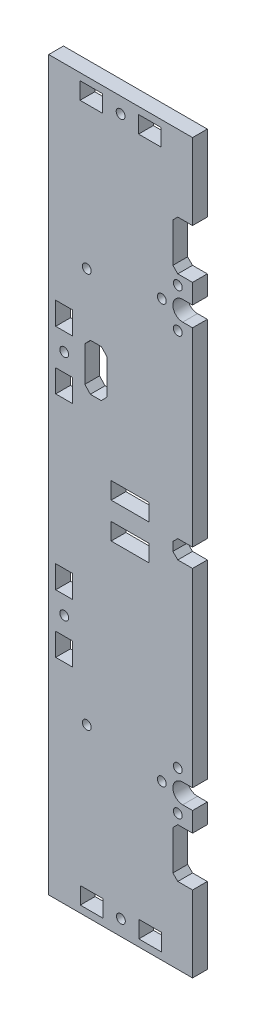
SolidWorks part; units mm, degrees
ref_plane "Plano frontal" through (0, 0, 0) normal (0, 0, 1) x (1, 0, 0)
ref_plane "Plano superior" through (0, 0, 0) normal (0, 1, 0) x (1, 0, 0)
ref_plane "Plano direito" through (0, 0, 0) normal (1, 0, 0) x (0, 0, -1)
sketch "Model" plane through (0, 0, 0) normal (0, 0, 1) x (1, 0, 0)
  line L0 (89.7713, 6.2321) -> (31.2713, 6.2321)
  line L1 (89.7713, 302.232) -> (89.7713, 271.232)
  line L2 (81.7713, 39.2321) -> (81.7713, 55.2321)
  line L3 (89.7713, 57.2321) -> (83.7713, 57.2321)
  line L4 (83.7713, 271.232) -> (89.7713, 271.232)
  line L5 (89.7713, 251.232) -> (89.7713, 243.232)
  line L6 (83.7713, 271.232) -> (81.7713, 269.232)
  line L7 (83.7713, 251.232) -> (89.7713, 251.232)
  line L8 (89.7713, 37.2321) -> (83.7713, 37.2321)
  line L9 (89.7713, 235.232) -> (89.7713, 157.982)
  line L10 (85.7713, 65.2321) -> (89.7713, 65.2321)
  line L11 (81.7713, 253.232) -> (81.7713, 269.232)
  line L12 (83.7713, 57.2321) -> (81.7713, 55.2321)
  line L13 (89.7713, 65.2321) -> (89.7713, 57.2321)
  line L14 (31.2713, 6.2321) -> (31.2713, 302.232)
  line L15 (85.7713, 243.232) -> (89.7713, 243.232)
  line L16 (31.2713, 302.232) -> (89.7713, 302.232)
  line L17 (83.7713, 37.2321) -> (81.7713, 39.2321)
  line L18 (85.7713, 235.232) -> (89.7713, 235.232)
  line L19 (85.7713, 73.2321) -> (89.7713, 73.2321)
  line L20 (89.7713, 37.2321) -> (89.7713, 6.2321)
  line L21 (83.7713, 251.232) -> (81.7713, 253.232)
  line L22 (77.1213, 9.0821) -> (77.1213, 15.9821)
  line L23 (44.0213, 299.382) -> (44.0213, 292.482)
  line L24 (72.0713, 143.582) -> (56.6713, 143.582)
  line L25 (41.0213, 91.332) -> (41.0213, 100.532)
  line L26 (53.2213, 292.482) -> (53.2213, 299.382)
  line L27 (77.0213, 299.382) -> (67.8213, 299.382)
  line L28 (77.0213, 292.482) -> (77.0213, 299.382)
  line L29 (34.1213, 217.132) -> (34.1213, 207.932)
  line L30 (34.1213, 115.132) -> (41.0213, 115.132)
  line L31 (41.0213, 207.932) -> (41.0213, 217.132)
  line L32 (44.0213, 292.482) -> (53.2213, 292.482)
  line L33 (34.1213, 91.332) -> (41.0213, 91.332)
  line L34 (44.1213, 15.9821) -> (44.1213, 9.0821)
  line L35 (34.1213, 184.132) -> (41.0213, 184.132)
  line L36 (53.2213, 299.382) -> (44.0213, 299.382)
  line L37 (41.0213, 193.332) -> (34.1213, 193.332)
  line L38 (34.1213, 124.332) -> (34.1213, 115.132)
  line L39 (41.0213, 100.532) -> (34.1213, 100.532)
  line L40 (56.6713, 157.982) -> (56.6713, 164.882)
  line L41 (53.3213, 15.9821) -> (44.1213, 15.9821)
  line L42 (41.0213, 115.132) -> (41.0213, 124.332)
  line L43 (34.1213, 100.532) -> (34.1213, 91.332)
  line L44 (77.1213, 15.9821) -> (67.9213, 15.9821)
  line L45 (72.0713, 164.882) -> (72.0713, 157.982)
  line L46 (53.3213, 9.0821) -> (53.3213, 15.9821)
  line L47 (67.8213, 299.382) -> (67.8213, 292.482)
  line L48 (72.0713, 157.982) -> (56.6713, 157.982)
  line L49 (67.9213, 9.0821) -> (77.1213, 9.0821)
  line L50 (67.8213, 292.482) -> (77.0213, 292.482)
  line L51 (41.0213, 184.132) -> (41.0213, 193.332)
  line L52 (44.1213, 9.0821) -> (53.3213, 9.0821)
  line L53 (34.1213, 207.932) -> (41.0213, 207.932)
  line L54 (56.6713, 164.882) -> (72.0713, 164.882)
  line L55 (34.1213, 193.332) -> (34.1213, 184.132)
  line L56 (67.9213, 15.9821) -> (67.9213, 9.0821)
  line L57 (56.6713, 143.582) -> (56.6713, 150.482)
  line L58 (56.6713, 150.482) -> (72.0713, 150.482)
  line L59 (72.0713, 150.482) -> (72.0713, 143.582)
  line L60 (41.0213, 217.132) -> (34.1213, 217.132)
  line L61 (41.0213, 124.332) -> (34.1213, 124.332)
  line L62 (54.9192, 207.6856) -> (52.6792, 210.0656)
  line L63 (52.6792, 191.0304) -> (48.1992, 191.0304)
  line L64 (52.6792, 191.0304) -> (54.9192, 193.4104)
  line L65 (45.9592, 193.4104) -> (48.1992, 191.0304)
  line L66 (45.9592, 207.6856) -> (45.9592, 193.4104)
  line L67 (48.1992, 210.0656) -> (45.9592, 207.6856)
  line L68 (48.1992, 210.0656) -> (52.6792, 210.0656)
  line L69 (54.9192, 207.6856) -> (54.9192, 193.4104)
  line L70 (83.7713, 157.982) -> (81.7713, 155.982)
  line L71 (83.7713, 150.482) -> (81.7713, 152.482)
  line L72 (81.7713, 152.482) -> (81.7713, 155.982)
  line L73 (89.7713, 157.982) -> (83.7713, 157.982)
  line L74 (89.7713, 150.482) -> (83.7713, 150.482)
  line L75 (89.7713, 150.482) -> (89.7713, 73.2321)
  circle A0 centre (60.6213, 12.5321) radius 1.8
  circle A1 centre (83.7713, 61.2332) radius 1.8
  circle A2 centre (77.2713, 69.2321) radius 1.8
  circle A3 centre (83.7713, 77.232) radius 1.8
  circle A4 centre (46.7713, 73.882) radius 1.8
  circle A5 centre (37.5713, 107.832) radius 1.8
  circle A6 centre (37.5713, 200.632) radius 1.8
  circle A7 centre (46.7713, 234.582) radius 1.8
  circle A8 centre (83.7713, 231.2331) radius 1.8
  circle A9 centre (77.2713, 239.232) radius 1.8
  circle A10 centre (83.7713, 247.232) radius 1.8
  circle A11 centre (60.5213, 295.932) radius 1.8
  arc A12 (85.7713, 243.232) -> (85.7713, 235.232) centre (85.7713, 239.232) ccw
  arc A13 (85.7713, 73.2321) -> (85.7713, 65.2321) centre (85.7713, 69.2321) ccw
extrude "Ressalto-extrusão1" add sketch "Model" along normal blind 6
ref_plane "Plano1" through (60.5713, 0, 0) normal (1, 0, 0) x (0, 0, -1)
ref_plane "Plano2" through (64.3713, 0, 0) normal (-1, 0, 0) x (0, 0, 1)
